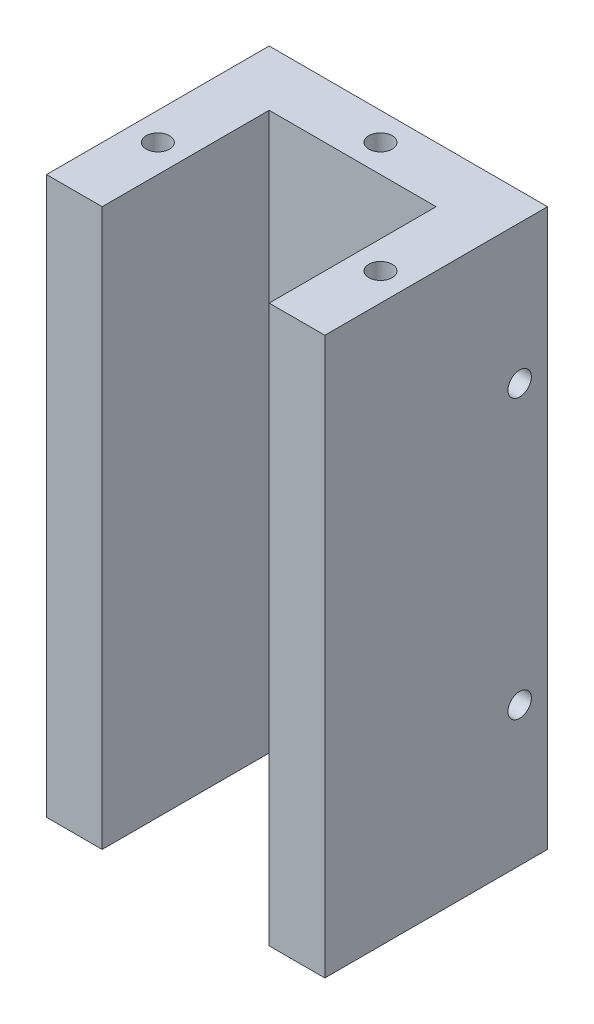
SolidWorks part; units mm, degrees
ref_plane "Front" through (0, 0, 0) normal (0, 0, 1) x (1, 0, 0)
ref_plane "Top" through (0, 0, 0) normal (0, 1, 0) x (1, 0, 0)
ref_plane "Right" through (0, 0, 0) normal (1, 0, 0) x (0, 0, -1)
sketch "Sketch1" plane through (0, 0, 0) normal (0, 1, 0) x (1, 0, 0)
  line L1 (-25, -20) -> (25, -20)
  line L2 (-25, -20) -> (-25, 20)
  line L3 (-25, 20) -> (25, 20)
  line L4 (25, -20) -> (25, 20)
  line L5 (-25, -20) -> (25, 20) construction
  line L6 (-25, 20) -> (25, -20) construction
  point P0 (0, 0)
  dimension "D1" = 50
  dimension "D2" = 40
extrude "Boss-Extrude1" add sketch "Sketch1" along normal blind 100
sketch "Sketch2" plane through (0, 100, 0) normal (0, 1, 0) x (1, 0, 0)
  line L0 (-25, -20) -> (25, -20) construction
  line L1 (-15, -20) -> (15, -20)
  line L2 (-15, -20) -> (-15, 10)
  line L3 (-15, 10) -> (15, 10)
  line L4 (15, -20) -> (15, 10)
  line L5 (-25, 20) -> (-25, -20) construction
  dimension "D1" = 30
  dimension "D2" = 30
  dimension "D3" = 10
extrude "Cut-Extrude1" cut sketch "Sketch2" against normal blind 100
sketch "Sketch3" plane through (0, 0, -20) normal (0, 0, -1) x (-1, 0, 0)
  line L0 (-25, 0) -> (25, 0) construction
  line L1 (-25, 100) -> (-25, 0) construction
  circle A0 centre (0, 25) radius 3.5
  circle A1 centre (0, 75) radius 3.5
  dimension "D1" = 7
  dimension "D2" = 7
  dimension "D3" = 50
  dimension "D4" = 25
  dimension "D5" = 25
extrude "Cut-Extrude2" cut sketch "Sketch3" against normal up to surface (10 mm away) up to face at (0, 50, -10)
hole_wizard "M5x0.8 Tapped Hole1" positions "Sketch5" profile "Sketch4" tap size "M5x0.8" standard "Ansi Metric"
sketch "Sketch5" plane through (0, 0, 0) normal (0, -1, 0) x (1, 0, 0)
  line L0 (-25, -20) -> (-25, 20) construction
  line L1 (25, 20) -> (25, -20) construction
  line L2 (-25, 20) -> (-15, 20) construction
  line L3 (15, 20) -> (25, 20) construction
  line L4 (25, -20) -> (-25, -20) construction
  point P0 (0, -15)
  point P1 (-20, 5)
  point P3 (20, 5)
  dimension "D1" = 5
  dimension "D2" = 5
  dimension "D3" = 15
  dimension "D4" = 15
  dimension "D5" = 5
  dimension "D6" = 25
sketch "Sketch4" plane through (0, 0, -15) normal (1, 0, 0) x (0, 0, -1)
  line L0 (0, 0) -> (0, 15.2618)
  line L1 (0, 15.2618) -> (2.1, 14)
  line L2 (2.1, 14) -> (2.1, 0)
  line L5 (2.1, 0) -> (0, 0)
  line L10 (0, 15.2618) -> (-2.1, 14) construction
  line L11 (0, -6.35) -> (0, 107.95) construction
  dimension "Tap Drill Dia." = 4.2
  dimension "Tap Drill Depth" = 14
  dimension "Drill Angle" = 118
cosmetic thread "Hole Thread1" parameters "D1"=10, "D2"=5
cosmetic thread "Hole Thread2" parameters "D1"=10, "D2"=5
cosmetic thread "Hole Thread3" parameters "D1"=10, "D2"=5
hole_wizard "M5x0.8 Tapped Hole2" positions "Sketch9" profile "Sketch8" tap size "M5x0.8" standard "Ansi Metric"
sketch "Sketch9" plane through (0, 100, 0) normal (0, 1, 0) x (-1, 0, 0)
  line L0 (-25, -20) -> (25, -20) construction
  line L1 (25, -20) -> (25, 20) construction
  point P1 (20, 5)
  point P4 (-20, 5)
  point P9 (0, -15)
  dimension "D1" = 5
  dimension "D2" = 25
sketch "Sketch8" plane through (-20, 100, 5) normal (1, 0, 0) x (0, 0, 1)
  line L0 (0, 0) -> (0, 15.2618)
  line L1 (0, 15.2618) -> (2.1, 14)
  line L2 (2.1, 14) -> (2.1, 0)
  line L5 (2.1, 0) -> (0, 0)
  line L10 (0, 15.2618) -> (-2.1, 14) construction
  line L11 (0, -6.35) -> (0, 107.95) construction
  dimension "Tap Drill Dia." = 4.2
  dimension "Tap Drill Depth" = 14
  dimension "Drill Angle" = 118
cosmetic thread "Hole Thread4" parameters "D1"=10, "D2"=5
cosmetic thread "Hole Thread5" parameters "D1"=10, "D2"=5
cosmetic thread "Hole Thread11" parameters "D1"=10, "D2"=5
hole_wizard "M5x0.8 Tapped Hole3" positions "Sketch11" profile "Sketch10" tap size "M5x0.8" standard "Ansi Metric"
sketch "Sketch11" plane through (25, 0, 0) normal (1, 0, 0) x (0, 0, -1)
  line L0 (20, 100) -> (20, 0) construction
  line L1 (-20, 100) -> (20, 100) construction
  line L2 (-20, 0) -> (20, 0) construction
  point P0 (15, 75)
  point P1 (15, 25)
  dimension "D1" = 5
  dimension "D2" = 25
  dimension "D3" = 5
  dimension "D4" = 25
sketch "Sketch10" plane through (25, 75, -15) normal (0, 1, 0) x (0, 0, -1)
  line L0 (0, 0) -> (0, 15.2618)
  line L1 (0, 15.2618) -> (2.1, 14)
  line L2 (2.1, 14) -> (2.1, 0)
  line L5 (2.1, 0) -> (0, 0)
  line L10 (0, 15.2618) -> (-2.1, 14) construction
  line L11 (0, -6.35) -> (0, 107.95) construction
  dimension "Tap Drill Dia." = 4.2
  dimension "Tap Drill Depth" = 14
  dimension "Drill Angle" = 118
cosmetic thread "Hole Thread7" parameters "D1"=10, "D2"=5
cosmetic thread "Hole Thread8" parameters "D1"=10, "D2"=5
hole_wizard "M5x0.8 Tapped Hole4" positions "Sketch13" profile "Sketch12" tap size "M5x0.8" standard "Ansi Metric"
sketch "Sketch13" plane through (-25, 0, 0) normal (-1, 0, 0) x (0, 0, 1)
  line L0 (-20, 100) -> (-20, 0) construction
  line L1 (-20, 0) -> (20, 0) construction
  line L2 (-20, 100) -> (20, 100) construction
  point P0 (-15, 75)
  point P1 (-15, 25)
  dimension "D1" = 5
  dimension "D2" = 5
  dimension "D3" = 25
  dimension "D4" = 25
sketch "Sketch12" plane through (-25, 75, -15) normal (0, 1, 0) x (0, 0, 1)
  line L0 (0, 0) -> (0, 15.2618)
  line L1 (0, 15.2618) -> (2.1, 14)
  line L2 (2.1, 14) -> (2.1, 0)
  line L5 (2.1, 0) -> (0, 0)
  line L10 (0, 15.2618) -> (-2.1, 14) construction
  line L11 (0, -6.35) -> (0, 107.95) construction
  dimension "Tap Drill Dia." = 4.2
  dimension "Tap Drill Depth" = 14
  dimension "Drill Angle" = 118
cosmetic thread "Hole Thread9" parameters "D1"=10, "D2"=5
cosmetic thread "Hole Thread10" parameters "D1"=10, "D2"=5
